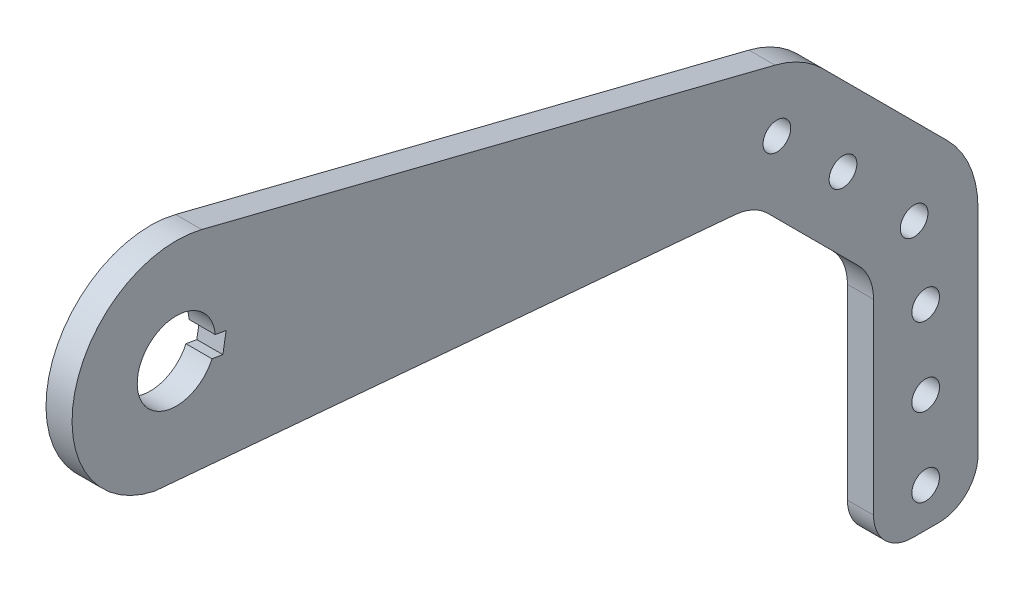
SolidWorks part; units mm, degrees
material "Plain Carbon Steel"
ref_plane "Front Plane" through (0, 0, 0) normal (0, 0, 1) x (1, 0, 0)
ref_plane "Top Plane" through (0, 0, 0) normal (0, 1, 0) x (1, 0, 0)
ref_plane "Right Plane" through (0, 0, 0) normal (1, 0, 0) x (0, 0, -1)
sketch "Sketch1" plane through (0, 0, 0) normal (1, 0, 0) x (0, 0, -1)
  line L0 (305.2991, -24.4357) -> (12.3959, 49.2644)
  line L2 (-10.6887, -49.6628) -> (281.6107, -75.2357)
  line L3 (281.6107, -75.2357) -> (339.725, -133.35)
  line L4 (339.725, -133.35) -> (339.725, -254)
  line L5 (339.725, -254) -> (390.6304, -254)
  line L6 (390.6304, -254) -> (390.6304, -109.767)
  line L7 (390.6304, -109.767) -> (305.2991, -24.4357)
  line L8 (281.6107, -75.2357) -> (305.2991, -24.4357) construction
  line L9 (339.725, -133.35) -> (390.6304, -109.767) construction
  circle A0 centre (0, 0) radius 19.05
  circle A1 centre (0, 0) radius 50.8
  dimension "D1" = 101.6
  dimension "D2" = 38.1
  dimension "D3" = 50.9054
  dimension "D4" = 135
  dimension "D5" = 135
  dimension "D6" = 254
  dimension "D7" = 339.725
  dimension "D8" = 120.65
  dimension "D9" = 50.8
  dimension "D10" = 110
  dimension "D11" = 110
extrude "Boss-Extrude1" add sketch "Sketch1" along normal blind 12.7
fillet "Fillet1" radius 25.4 2 edges at (6.35, -133.35, -339.725) (6.35, -75.2357, -281.6107)
fillet "Fillet2" radius 50.8 2 edges at (6.35, -109.767, -390.6304) (6.35, -24.4357, -305.2991)
hole_wizard "1/2 Clearance Hole1" positions "Sketch3" profile "Sketch2" hole size "1/2" standard "ANSI Inch"
sketch "Sketch3" plane through (12.7, 0, 0) normal (1, 0, 0) x (0, 0, -1)
  line L8 (306.1083, -63.8122) -> (350.246, -107.95)
  line L9 (365.125, -143.871) -> (365.125, -254)
  line L10 (306.1083, -63.8122) -> (350.246, -107.95)
  line L11 (365.125, -143.871) -> (365.125, -254)
  line L12 (339.725, -254) -> (390.6304, -254) construction
  arc A4 (365.125, -143.871) -> (350.246, -107.95) centre (314.325, -143.871) ccw
  arc A5 (365.125, -143.871) -> (350.246, -107.95) centre (314.325, -143.871) ccw
  point P34 (365.125, -234.95)
  point P36 (365.125, -196.85)
  point P38 (365.125, -158.75)
  point P40 (359.5071, -120.65)
  point P42 (324.846, -82.55)
  dimension "D2" = 38.1
  dimension "D3" = 19.05
  dimension "D4" = 38.1
  dimension "D5" = 38.1
  dimension "D6" = 38.1
  dimension "D1" = 25.4
sketch "Sketch2" plane through (12.7, -234.95, -365.125) normal (0, 1, 0) x (0, 0, -1)
  line L0 (0, 0) -> (0, 42.1535)
  line L1 (0, 42.1535) -> (6.7462, 38.1)
  line L2 (6.7462, 38.1) -> (6.7462, 0)
  line L5 (6.7462, 0) -> (0, 0)
  line L10 (0, 42.1535) -> (-6.7462, 38.1) construction
  line L11 (0, -6.35) -> (0, 107.95) construction
  dimension "Hole Dia." = 13.4925
  dimension "Hole Depth" = 38.1
  dimension "Drill Angle" = 118
fillet "Fillet3" radius 19.05 2 edges at (6.35, -254, -390.6304) (6.35, -254, -339.725)
sketch "Sketch4" plane through (12.7, 0, 0) normal (1, 0, 0) x (0, 0, -1)
  line L0 (23.4788, -3.9725) -> (24.2733, 0.7233)
  line L1 (0, 0) -> (282.0475, -47.7211) construction
  line L2 (272.401, -74.4299) -> (291.694, -21.0124) construction
  line L3 (24.2733, 0.7233) -> (14.8818, 2.3123)
  line L4 (14.8818, 2.3123) -> (13.2928, -7.0793)
  line L5 (13.2928, -7.0793) -> (22.6843, -8.6683)
  line L6 (22.6843, -8.6683) -> (23.4788, -3.9725)
  line L7 (19.5775, 1.5178) -> (17.9885, -7.8738) construction
  dimension "D1" = 9.525
  dimension "D2" = 19.05
  dimension "D3" = 9.525
extrude "Cut-Extrude1" cut sketch "Sketch4" against normal through all
hole_wizard "1/2 Clearance Hole2" positions "Sketch6" profile "Sketch5" hole size "1/2" standard "ANSI Inch" end condition through all
sketch "Sketch6" plane through (12.7, 0, 0) normal (1, 0, 0) x (0, 0, -1)
  line L0 (280.9217, -76.713) -> (304.3609, -26.0897) construction
  arc A0 (288.1478, -81.7728) -> (272.401, -74.4299) centre (270.1872, -99.7333) ccw construction
  arc A1 (315.2192, -34.3558) -> (291.694, -21.0124) centre (279.2982, -70.2768) ccw construction
  point P10 (292.6413, -51.4014)
sketch "Sketch5" plane through (12.7, -51.4014, -292.6413) normal (0, 1, 0) x (0, 0, -1)
  line L0 (0, 0) -> (0, 12.7)
  line L1 (0, 12.7) -> (6.7462, 12.7)
  line L2 (6.7462, 12.7) -> (6.7462, 0)
  line L5 (6.7462, 0) -> (0, 0)
  line L11 (0, -6.35) -> (0, 107.95) construction
  dimension "Thru Hole Dia." = 13.4925
  dimension "Thru Hole Depth" = 12.7
